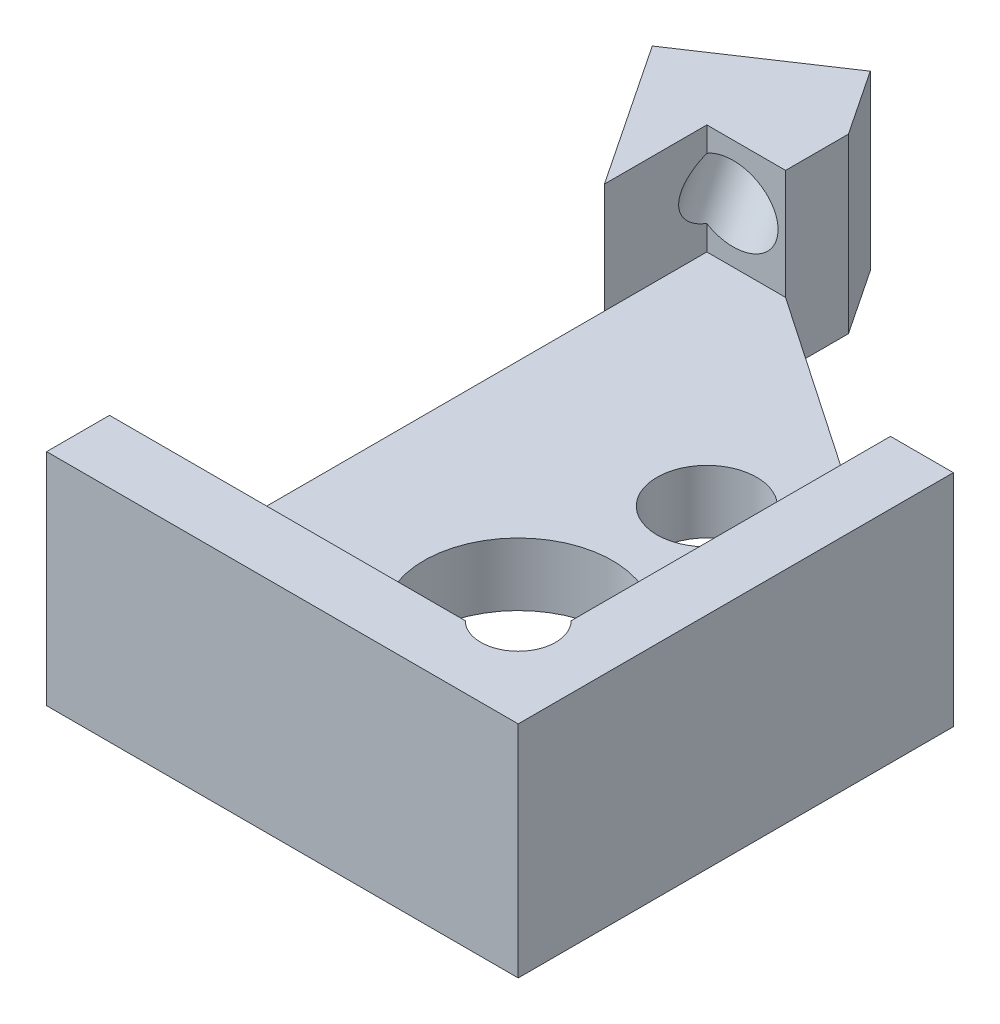
SolidWorks part; units mm, degrees
ref_plane "Front Plane" through (0, 0, 0) normal (0, 0, 1) x (1, 0, 0)
ref_plane "Top Plane" through (0, 0, 0) normal (0, 1, 0) x (1, 0, 0)
ref_plane "Right Plane" through (0, 0, 0) normal (1, 0, 0) x (0, 0, -1)
sketch "Sketch1" plane through (0, 0, 0) normal (0, 1, 0) x (1, 0, 0)
  line L7 (4.25, 5.75) -> (-4.25, 5.75)
  line L8 (4.25, 5.75) -> (4.25, -5.75)
  line L9 (4.25, -5.75) -> (-4.25, -5.75)
  line L10 (-4.25, 5.75) -> (-4.25, -5.75)
  line L11 (4.25, 5.75) -> (-4.25, -5.75) construction
  line L12 (4.25, -5.75) -> (-4.25, 5.75) construction
  point P0 (0, 0)
  point P6 (0, 0)
  dimension "D1" = 8.5
  dimension "D2" = 11.5
extrude "Boss-Extrude1" add sketch "Sketch1" along normal blind 3.5
sketch "Sketch2" plane through (0, 3.5, 0) normal (0, 1, 0) x (1, 0, 0)
  line L0 (-4.25, 5.75) -> (-4.25, -5.75) construction
  line L1 (3.25, 4.75) -> (-3.25, 4.75)
  line L2 (3.25, 4.75) -> (3.25, -4.75)
  line L3 (3.25, -4.75) -> (-3.25, -4.75)
  line L4 (-3.25, 4.75) -> (-3.25, -4.75)
  line L5 (3.25, 4.75) -> (-3.25, -4.75) construction
  line L6 (3.25, -4.75) -> (-3.25, 4.75) construction
  line L7 (4.25, 5.75) -> (-4.25, 5.75) construction
  point P0 (0, 0)
  dimension "D1" = 1
  dimension "D2" = 1
extrude "Cut-Extrude1" cut sketch "Sketch2" against normal offset from surface (14.489 mm away) 1
sketch "Sketch3" plane through (0, 1, 0) normal (0, 1, 0) x (1, 0, 0)
  line L0 (-3.25, -4.75) -> (3.25, -4.75) construction
  line L1 (3.25, -4.75) -> (3.25, 4.75) construction
  circle A0 centre (0.25, -1.75) radius 1.5
  dimension "D1" = 3
  dimension "D2" = 3
  dimension "D3" = 3
extrude "Cut-Extrude2" cut sketch "Sketch3" against normal through all
sketch "Sketch6" plane through (0, 3.5, 0) normal (0, 1, 0) x (1, 0, 0)
  line L0 (3.25, -4.75) -> (3.25, 4.75) construction
  line L2 (-3.25, -4.75) -> (3.25, -4.75) construction
  line L3 (3.25, -4.3291) -> (2.8291, -4.3291) construction
  line L4 (2.8291, -4.3291) -> (2.8291, -4.75) construction
  circle A3 centre (2.8291, -4.3291) radius 0.5953
  dimension "D1" = 1.1906
extrude "Cut-Extrude5" cut sketch "Sketch6" against normal up to surface (2.5 mm away) up to face at (0.25, 1, 3.25)
sketch "Sketch7" plane through (0, 1, 0) normal (0, 1, 0) x (1, 0, 0)
  line L0 (2.125, 1.25) -> (-1.625, 1.25) construction
  line L1 (-1.625, 1.25) -> (-1.625, -3.5) construction
  line L2 (-1.625, -3.5) -> (2.125, -3.5) construction
  line L3 (2.125, -3.5) -> (2.125, 1.25) construction
  line L4 (0.25, 1.25) -> (0.25, -1.75) construction
  circle A0 centre (0.25, 1.25) radius 0.7937
  circle A2 centre (-1.625, -3.5) radius 0.7938
  circle A3 centre (2.125, -3.5) radius 0.7938
  circle A4 centre (0.25, -1.75) radius 1.5 construction
  dimension "D1" = 1.5875
  dimension "D2" = 3.75
  dimension "D3" = 3
  dimension "D4" = 1.75
extrude "Cut-Extrude6" cut sketch "Sketch7" against normal through all
sketch "Sketch9" plane through (0, 3.5, 0) normal (0, 1, 0) x (1, 0, 0)
  line L0 (-2.6906, 6.7896) -> (-4.7708, 5.4028)
  line L1 (-3.4116, 4.6422) -> (-4.0015, 4.249)
  line L2 (-3.4116, 4.6422) -> (-2.5113, 5.2425)
  line L3 (-2.6906, 6.7896) -> (-1.9214, 5.6357)
  line L4 (3.25, -4.75) -> (-2.75, 4.25) construction
  line L5 (3.25, -4.75) -> (-2.75, -4.75) construction
  line L6 (-3.25, -4.75) -> (2.4081, -4.75) construction
  line L8 (-2.75, -4.75) -> (-2.75, 4.25) construction
  line L9 (-2.75, 4.25) -> (3.25, 4.25) construction
  line L10 (3.25, -3.9081) -> (3.25, 4.75) construction
  line L11 (3.25, 4.25) -> (3.25, -4.75) construction
  line L12 (-2.75, 3.6498) -> (-1.8497, 4.25) construction
  line L13 (-2.75, 3.6498) -> (-3.4116, 4.6422) construction
  line L14 (-2.2998, 3.9499) -> (-2.9615, 4.9423) construction
  line L15 (-1.9214, 5.6357) -> (-2.5113, 5.2425)
  line L16 (-4.0015, 4.249) -> (-4.7708, 5.4028)
  line L17 (-2.9615, 4.9423) -> (-3.7307, 6.0962) construction
  arc A0 (2.4081, -4.75) -> (3.25, -3.9081) centre (2.8291, -4.3291) ccw construction
  dimension "D1" = 6
  dimension "D2" = 9
  dimension "D3" = 1.082
  dimension "D4" = 2.5
extrude "Boss-Extrude2" add sketch "Sketch9" against normal up to surface (3.5 mm away) up to face at (2.125, 0, 4.2938)
sketch "Sketch14" plane through (0, 3.5, 0) normal (0, 1, 0) x (1, 0, 0)
  line L1 (-6.2326, 2.1835) -> (-0.2674, 2.1835)
  line L2 (-6.2326, 2.1835) -> (-6.2326, 7.3165)
  line L3 (-6.2326, 7.3165) -> (-0.2674, 7.3165)
  line L4 (-0.2674, 2.1835) -> (-0.2674, 7.3165)
  line L5 (-6.2326, 2.1835) -> (-0.2674, 7.3165) construction
  line L6 (-6.2326, 7.3165) -> (-0.2674, 2.1835) construction
  point P0 (-3.25, 4.75)
extrude "Cut-Extrude8" cut sketch "Sketch14" against normal blind 0.75
sketch "Sketch10" plane through (-3.9615, 0, -5.9423) normal (-0.5547, 0, -0.8321) x (-0.8321, 0, 0.5547)
  line L0 (-0.2774, 1) -> (-0.2774, 1.875) construction
  line L1 (-1.5274, 2.75) -> (0.9726, 2.75) construction
  line L2 (-0.2774, 1.875) -> (-0.2774, 2.75) construction
  line L4 (-0.2774, 1) -> (-0.2774, 0) construction
  line L5 (-1.5274, 0) -> (0.9726, 0) construction
  dimension "D1" = 1
hole_wizard "Tap Drill for #0-80 Tap1" positions "Sketch12" profile "Sketch11" hole size "#0-80" standard "ANSI Inch"
sketch "Sketch12" plane through (-3.9615, 0, -5.9423) normal (-0.5547, 0, -0.8321) x (-0.8321, 0, 0.5547)
  point P0 (-0.2774, 1.875)
sketch "Sketch11" plane through (-3.7307, 1.875, -6.0962) normal (0, 1, 0) x (-0.8321, 0, 0.5547)
  line L0 (0, 0) -> (0, 7.4679)
  line L1 (0, 7.4679) -> (0.5956, 7.11)
  line L2 (0.5956, 7.11) -> (0.5956, 0)
  line L5 (0.5956, 0) -> (0, 0)
  line L10 (0, 7.4679) -> (-0.5956, 7.11) construction
  line L11 (0, -6.35) -> (0, 107.95) construction
  dimension "Hole Dia." = 1.1913
  dimension "Hole Depth" = 7.11
  dimension "Drill Angle" = 118
sketch "Sketch13" plane through (0, 3.5, 0) normal (0, 1, 0) x (1, 0, 0)
  line L0 (-1.9976, 5.75) -> (-1.9976, 4.75)
  line L2 (-1.625, -3.5) -> (-3.25, -3.5) construction
  line L3 (3.25, 1.1708) -> (4.25, 1.1708)
  line L4 (4.25, -5.75) -> (4.25, 5.75) construction
  line L5 (4.25, 1.1708) -> (4.25, 5.75)
  line L6 (4.25, 5.75) -> (-1.9976, 5.75)
  line L7 (-4.25, 4.6217) -> (-3.25, 3.1217)
  line L8 (-3.25, 2.1835) -> (-3.25, -4.75) construction
  line L9 (-4.25, 2.1835) -> (-4.25, -5.75) construction
  line L10 (-3.25, 3.1217) -> (-3.25, -5.75)
  line L11 (-4.25, -5.75) -> (4.25, -5.75) construction
  line L12 (-3.25, -5.75) -> (-4.25, -5.75)
  line L13 (-4.25, -5.75) -> (-4.25, 4.6217)
  line L15 (-4.7708, 5.4028) -> (-4.25, 4.6217) construction
  line L17 (-1.9976, 4.75) -> (3.25, 1.1708)
  line L18 (3.25, -3.9081) -> (3.25, 4.75) construction
  line L20 (0.25, 1.25) -> (1.1656, 2.5925) construction
  line L23 (3.25, 4.75) -> (-0.2674, 4.75) construction
extrude "Cut-Extrude7" cut sketch "Sketch13" against normal up to next
